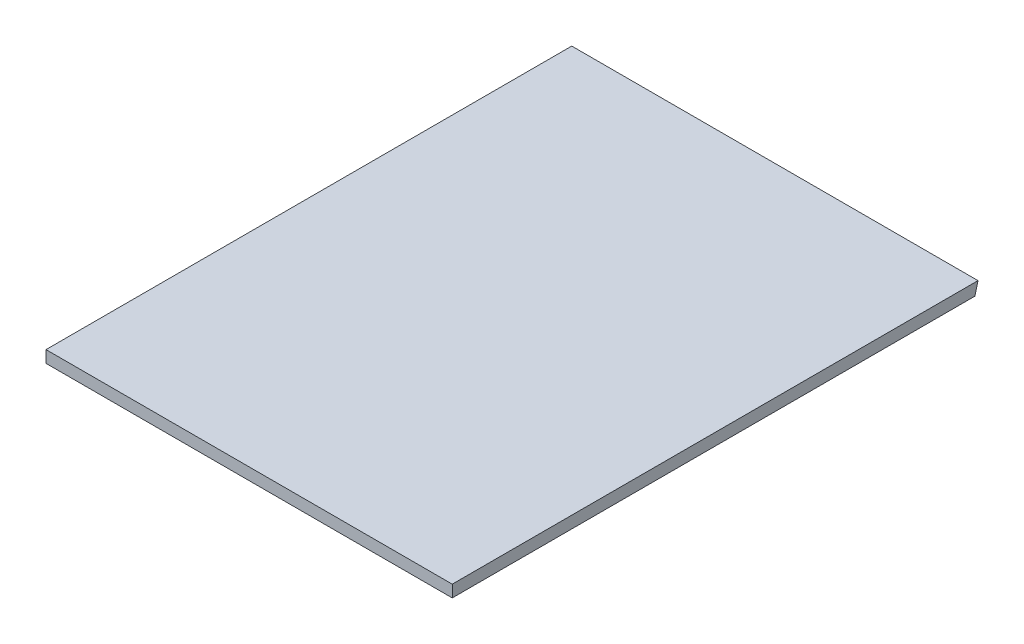
SolidWorks part; units mm, degrees
material "Balsa"
ref_plane "Alzado" through (0, 0, 0) normal (0, 0, 1) x (1, 0, 0)
ref_plane "Planta" through (0, 0, 0) normal (0, 1, 0) x (1, 0, 0)
ref_plane "Vista lateral" through (0, 0, 0) normal (1, 0, 0) x (0, 0, -1)
sketch "Croquis1" plane through (0, 0, 0) normal (0, 1, 0) x (1, 0, 0)
  line L1 (-170, 11.0314) -> (0, 11.0314)
  line L2 (-170, 11.0314) -> (-170, -208.9686)
  line L3 (-170, -208.9686) -> (0, -208.9686)
  line L4 (0, 11.0314) -> (0, -208.9686)
  dimension "D1" = 220
  dimension "D2" = 170
extrude "Saliente-Extruir1" add sketch "Croquis1" along normal blind 5
sketch "Croquis2" plane through (0, 0, 0) normal (1, 0, 0) x (0, 0, -1)
  line L0 (11.0314, 5) -> (7.7362, -7.522)
  line L3 (-208.9686, 5) -> (11.0314, 5) construction
  dimension "D1" = 75.256
extrude "Cortar-Extruir1" cut sketch "Croquis2" against normal through all and the other way through all
